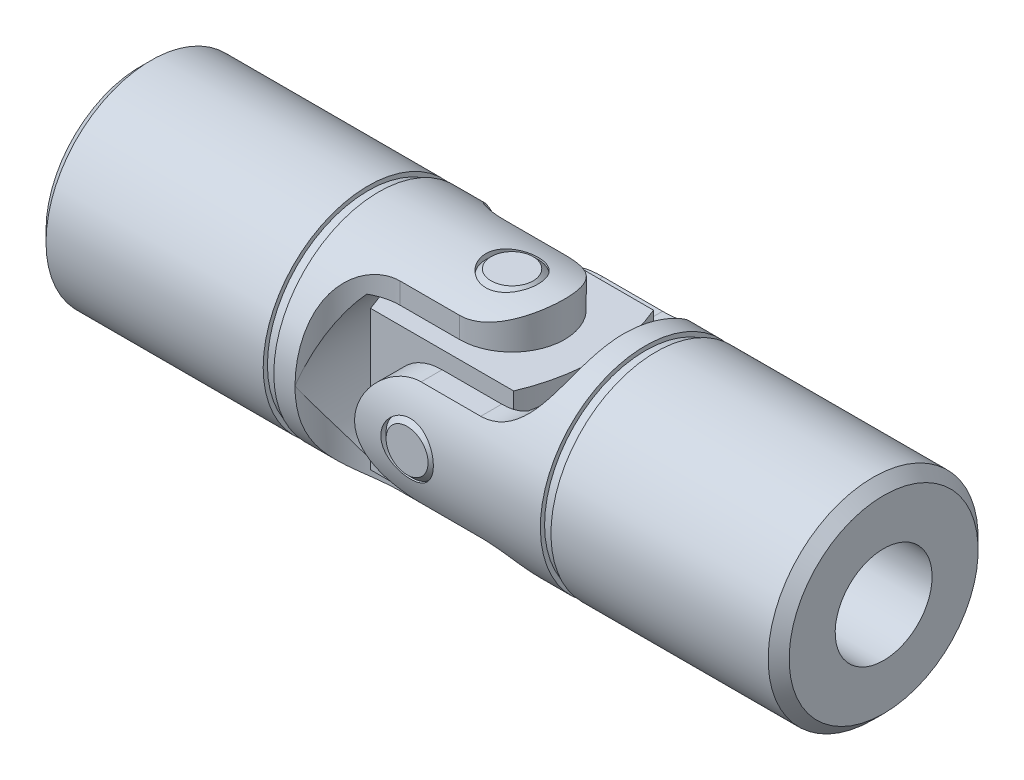
SolidWorks part; units mm, degrees
ref_plane "Front Plane" through (0, 0, 0) normal (0, 0, 1) x (1, 0, 0)
ref_plane "Top Plane" through (0, 0, 0) normal (0, 1, 0) x (1, 0, 0)
ref_plane "Right Plane" through (0, 0, 0) normal (1, 0, 0) x (0, 0, -1)
sketch "Sketch0" plane through (0, 0, 0) normal (0, 1, 0) x (1, 0, 0)
  line L0 (-36.5125, 0) -> (36.5125, 0) construction
  line L1 (-36.5125, 10.3187) -> (-36.5125, -10.3187) construction
  line L2 (-14.2875, 4.7625) -> (-14.2875, -4.7625) construction
  line L3 (-14.2875, 4.7625) -> (-9.525, 0) construction
  line L4 (-9.525, 0) -> (-14.2875, -4.7625) construction
  line L5 (-11.9062, 2.3812) -> (-11.9062, -2.3812) construction
  point P7 (-14.2875, 0)
  point P8 (0, 0)
  point P12 (-11.9062, 0)
sketch "Sketch1" plane through (0, 0, 0) normal (0, 1, 0) x (1, 0, 0)
  line L0 (-36.5125, 10.3187) -> (-14.1387, 10.3187)
  line L1 (5.1594, 10.3188) -> (5.1594, 0)
  line L2 (5.1594, 0) -> (-36.5125, 0)
  line L3 (-36.5125, 0) -> (-36.5125, 10.3187)
  line L4 (-36.5125, 10.3187) -> (-36.5125, -10.3187) construction
  line L5 (-36.5125, 0) -> (36.5125, 0) construction
  line L6 (-13.0969, 10.3187) -> (5.1594, 10.3188)
  line L7 (-13.0969, 2.3812) -> (-13.0969, 9.902) construction
  line L8 (-14.1387, 10.3187) -> (-14.1387, 9.902)
  line L9 (-14.1387, 9.902) -> (-13.0969, 9.902)
  line L10 (-13.0969, 10.3187) -> (-13.0969, 9.902)
  line L11 (0, 0) -> (10.3187, 0) construction
  line L12 (-11.9062, 2.3812) -> (-14.2875, 2.3812) construction
  line L13 (-14.2875, 4.7625) -> (-14.2875, -4.7625) construction
  circle A0 centre (0, 0) radius 10.3187 construction
  dimension "D1" = 1.0418
  dimension "D2" = 0.4167
  dimension "D3" = 41.6719
revolve "Revolve1" add sketch "Sketch1" angle 360 about L0
chamfer "Chamfer1" distance 1.0319 angle 45 1 edges at (-36.5125, 0, 10.3187)
sketch "Sketch2" plane through (0, 0, 0) normal (0, 1, 0) x (1, 0, 0)
  line L0 (-13.0969, 10.3188) -> (-11.0133, 10.3188) construction
  line L1 (-13.0969, 10.3187) -> (5.1594, 10.3188) construction
  line L2 (5.1594, 10.3188) -> (-13.0969, 10.3188) construction
  line L4 (-36.5125, 0) -> (5.1594, 0) construction
  line L5 (-11.0133, 10.3188) -> (10.3187, 10.3187)
  line L6 (10.3187, 10.3187) -> (10.3187, -10.3187)
  line L7 (10.3187, -10.3187) -> (-11.0133, -10.3188)
  line L8 (0, 5.1594) -> (0, 0) construction
  line L9 (0, 5.1594) -> (-5.8539, 5.1594)
  line L10 (-11.0133, 10.3188) -> (-11.0133, -10.3188) construction
  line L11 (0, -5.1594) -> (-5.8539, -5.1594)
  arc A0 (-11.0133, 10.3188) -> (-5.8539, 5.1594) centre (-5.8539, 10.3188) ccw
  arc A1 (0, -5.1594) -> (0, 5.1594) centre (0, 0) ccw
  arc A2 (-5.8539, -5.1594) -> (-11.0133, -10.3188) centre (-5.8539, -10.3188) ccw
  dimension "D1" = 10.3187
  dimension "D2" = 2.0836
extrude "Extrude1" cut sketch "Sketch2" against normal through all and the other way through all
sketch "Sketch3" plane through (0, 0, 0) normal (0, 0, 1) x (1, 0, 0)
  line L0 (-8.4336, 6.8723) -> (-11.0133, 4.2926) construction
  line L1 (-8.4336, 6.8723) -> (10.3187, 6.8723)
  line L2 (-11.0133, 4.2926) -> (-11.0133, -4.2926) construction
  line L3 (-8.4336, -6.8723) -> (10.3187, -6.8723)
  line L4 (10.3187, 6.8723) -> (10.3187, -6.8723)
  line L5 (-11.0133, -4.2926) -> (-8.4336, -6.8723) construction
  line L6 (-11.0133, 0) -> (-5.8539, 0) construction
  line L7 (-5.8539, -8.9363) -> (-5.8539, 8.9363) construction
  line L8 (10.3187, 0) -> (-11.0133, 0) construction
  line L9 (-8.4336, 0) -> (-8.4336, 6.8723) construction
  arc A0 (-8.4336, 6.8723) -> (-8.4336, -6.8723) centre (-0.5696, 0) ccw
  dimension "D1" = 13.7446
extrude "Extrude3" cut sketch "Sketch3" against normal through all and the other way through all
sketch "Sketch4" plane through (-36.5125, 0, 0) normal (-1, 0, 0) x (0, 0, 1)
  circle A0 centre (0, 0) radius 4.7625
extrude "Extrude4" cut sketch "Sketch4" against normal up to vertex (22.225 mm away) up to point (-14.2875, 0, -4.7625)
sketch "Sketch5" plane through (-14.2875, 0, 0) normal (-1, 0, 0) x (0, 0, 1)
  circle A0 centre (0, 0) radius 4.7625 construction
  circle A1 centre (0, 0) radius 4.7625
extrude "Extrude5" cut sketch "Sketch5" against normal through all draft 45
sketch "Sketch6" plane through (0, 0, 0) normal (0, 1, 0) x (1, 0, 0)
  line L0 (-36.5125, 0) -> (36.5125, 0) construction
  line L1 (5.1594, 0) -> (2.5797, 0) construction
  line L2 (2.5797, 0) -> (0, 0) construction
  circle A0 centre (0, 0) radius 2.5797
  arc A1 (0, -5.1594) -> (0, 5.1594) centre (0, 0) ccw construction
  dimension "D1" = 5.1594
extrude "Extrude6" cut sketch "Sketch6" against normal through all and the other way through all
mirror "Mirror1" about plane through (0, 0, 0) normal (1, 0, 0) of bodies 109 122
move or copy body "Body-Move/Copy1" bodies to move or copy 110 copy no rotation origin (0, 0, 0) rotation axis (1, 0, 0) rotation angle 90
sketch "Sketch18" plane through (0, 0, 0) normal (0, 1, 0) x (1, 0, 0)
  line L0 (-47.625, -4.7625) -> (-14.2875, -4.7625)
  line L3 (-47.625, 4.7625) -> (-14.2875, 4.7625)
  line L4 (-14.2875, 4.7625) -> (-14.2875, -4.7625)
  line L5 (14.2875, 4.7625) -> (14.2875, -4.7625)
  line L6 (14.2875, -4.7625) -> (36.5125, -4.7625)
  line L7 (14.2875, 4.7625) -> (36.5125, 4.7625)
  line L8 (0, 0) -> (14.2875, 0) construction
  line L9 (36.5125, -9.2869) -> (36.5125, 9.2869) construction
  line L11 (-14.2875, -4.7625) -> (-14.2875, 4.7625) construction
sketch "Sketch10" plane through (0, 0, 0) normal (0, 0, 1) x (1, 0, 0)
  line L0 (-8.4336, 6.8723) -> (8.4336, -6.8723) construction
  line L1 (-8.4336, 6.8723) -> (8.4336, 6.8723)
  line L2 (-8.4336, 6.8723) -> (-8.4336, -6.8723)
  line L3 (-8.4336, -6.8723) -> (8.4336, -6.8723)
  line L4 (8.4336, 6.8723) -> (8.4336, -6.8723)
  line L5 (0, 6.8723) -> (5.1594, 6.8723) construction
extrude "Extrude10" add sketch "Sketch10" against normal up to surface and the other way up to surface separate body up to face at (0, 2.5797, -6.8723) other way up to face at (0, -2.5797, 6.8723)
sketch "Sketch20" plane through (0, 6.8723, 0) normal (0, 1, 0) x (1, 0, 0)
  line L4 (8.4336, 6.8723) -> (-8.4336, 6.8723) construction
  line L5 (8.4336, -6.8723) -> (-8.4336, -6.8723) construction
  line L6 (-8.4336, 6.8723) -> (-8.4336, -6.8723) construction
  line L7 (8.4336, 6.8723) -> (8.4336, -6.8723) construction
  line L8 (9.4496, -7.8883) -> (9.4496, 7.8883)
  line L9 (9.4496, 7.8883) -> (-9.4496, 7.8883)
  line L10 (-9.4496, 7.8883) -> (-9.4496, -7.8883)
  line L11 (-9.4496, -7.8883) -> (9.4496, -7.8883)
  line L12 (9.4496, -7.8883) -> (9.4496, 7.8883)
  line L13 (9.4496, 7.8883) -> (7.028, 7.8883)
  line L14 (-9.4496, 7.8883) -> (-9.4496, -7.8883)
  line L15 (-9.4496, -7.8883) -> (-7.028, -7.8883)
  line L16 (-7.028, 6.8723) -> (-7.028, 7.8883)
  line L17 (7.028, 6.8723) -> (7.028, 7.8883)
  line L18 (7.028, -6.8723) -> (7.028, -7.8883)
  line L19 (-7.028, -6.8723) -> (-7.028, -7.8883)
  line L20 (-7.028, 7.8883) -> (-9.4496, 7.8883)
  line L21 (7.028, -7.8883) -> (9.4496, -7.8883)
  line L22 (-36.5125, 0) -> (5.1594, 0) construction
  line L23 (8.4336, 6.8723) -> (-8.4336, 6.8723) construction
  arc A0 (7.028, 6.8723) -> (7.028, -6.8723) centre (-9.0693, 0) cw
  arc A1 (-7.028, 6.8723) -> (-7.028, -6.8723) centre (9.0693, 0) ccw
  dimension "D2" = 16.8672
  dimension "D3" = 1.4056
extrude "Cut-Extrude2" cut sketch "Sketch20" against normal through all
sketch "Sketch13" plane through (0, 0, 0) normal (0, 1, 0) x (1, 0, 0)
  circle A0 centre (0, 0) radius 2.5797 construction
  circle A1 centre (0, 0) radius 2.5797
extrude "Extrude13" cut sketch "Sketch13" against normal through all and the other way through all
sketch "Sketch14" plane through (0, 0, 0) normal (0, 1, 0) x (1, 0, 0)
  circle A1 centre (0, 0) radius 2.5797
  circle A2 centre (0, 0) radius 2.5797
  dimension "D1" = 0
extrude "Extrude14" add sketch "Sketch14" along normal mid plane 20.6375 separate body
sketch "Sketch15" plane through (0, 0, 0) normal (0, 0, 1) x (1, 0, 0)
  circle A0 centre (0, 0) radius 2.5797 construction
  circle A1 centre (0, 0) radius 2.5797
extrude "Extrude15" cut sketch "Sketch15" against normal through all and the other way through all
sketch "Sketch16" plane through (0, 0, 0) normal (0, 0, 1) x (1, 0, 0)
  circle A1 centre (0, 0) radius 2.5797
  circle A2 centre (0, 0) radius 2.5797
  dimension "D1" = 0
extrude "Extrude16" add sketch "Sketch16" along normal mid plane 20.6375
chamfer "Chamfer3" distance 0.5159 angle 45 4 edges at (0, -10.3187, 2.5797) (0, 10.3187, 2.5797) (2.5797, 0, 10.3187) (2.5797, 0, -10.3187)
move or copy body "Body-Move/Copy2" [suppressed] bodies to move or copy 111 copy no rotation origin (0, 0, 0) rotation axis (0, 0, -1) rotation angle 15
equation "\"D2@Sketch3\" = \"D1@Sketch3\" / 4"
equation "\"D1@Extrude14\" = \"OD@Sketch0\""
equation "\"D1@Extrude16\" = \"D1@Extrude14\""
equation "\"D1@Sketch3\" = \"OD@Sketch0\"*.666"
equation "\"D1@Sketch1\" = \"D3@Sketch1\"*.025"
equation "\"D2@Sketch1\" = \"D1@Sketch1\"/2.5"
equation "\"D1@Chamfer1\" = \"OD@Sketch0\"/20"
equation "\"D1@Chamfer3\" = \"D1@Chamfer1\"*.50"
equation "\"D2@Sketch2\" = \"D1@Sketch1\"*2"
equation "\"D3@Sketch20\" = \"D2@Sketch20\"/12"
